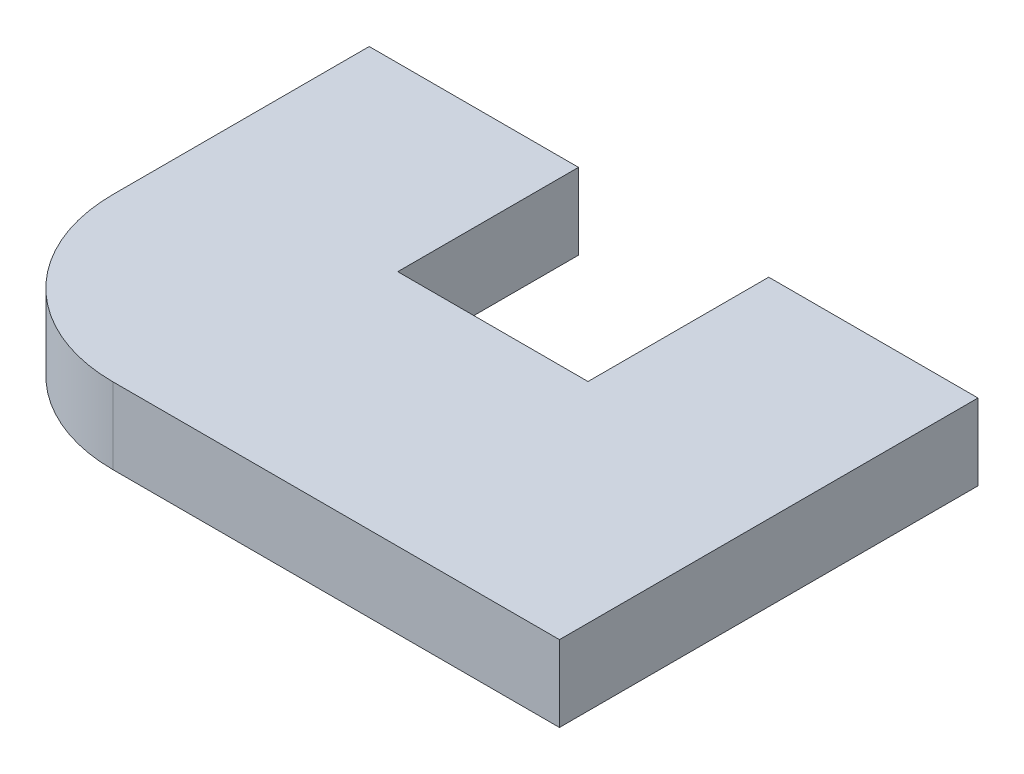
SolidWorks part; units mm, degrees
material "Ti-6Al-4VSolution treated and aged (SS)"
ref_plane "Front Plane" through (0, 0, 0) normal (0, 0, 1) x (1, 0, 0)
ref_plane "Top Plane" through (0, 0, 0) normal (0, 1, 0) x (1, 0, 0)
ref_plane "Right Plane" through (0, 0, 0) normal (1, 0, 0) x (0, 0, -1)
sketch "Sketch1" plane through (0, 0, 0) normal (0, 1, 0) x (1, 0, 0)
  line L1 (30.3553, -110) -> (55, -110)
  line L2 (-55, -24.6447) -> (-55, 110)
  line L3 (-55, 110) -> (55, 110)
  line L4 (55, -110) -> (55, 110)
  line L5 (-55, -110) -> (55, 110) construction
  line L6 (-55, 110) -> (55, -110) construction
  line L7 (55, -110) -> (155, -110)
  line L8 (55, -110) -> (55, 15)
  line L9 (55, 15) -> (155, 15)
  line L10 (155, -110) -> (155, 15)
  line L11 (155, -110) -> (265, -110)
  line L12 (155, -110) -> (155, 110)
  line L13 (155, 110) -> (265, 110)
  line L14 (265, -110) -> (265, 110)
  line L15 (-55, -110) -> (-30, -110) construction
  line L16 (-55, -110) -> (-55, -85) construction
  line L17 (-55, -85) -> (-30, -85) construction
  line L18 (-30, -110) -> (-30, -85) construction
  arc A0 (30.3553, -110) -> (-55, -24.6447) centre (30.3553, -24.6447) cw
  point P0 (0, 0)
  dimension "D1" = 25
  dimension "D2" = 220
  dimension "D3" = 100
  dimension "D4" = 125
  dimension "D5" = 210
  dimension "D6" = 25
extrude "Boss-Extrude1" add sketch "Sketch1" along normal blind 40 contours L1 L4 L3 L2 | L7 L10 L9 L4 | L11 L14 L13 L12 L10
fillet "Fillet1" [suppressed] radius 10
fillet "Fillet2" [suppressed] radius 20
sketch "Sketch2" plane through (0, 0, 0) normal (0, 1, 0) x (1, 0, 0)
  line L0 (55, -110) -> (155, -110) construction
  line L2 (55, 15) -> (155, 15) construction
  line L4 (155, -110) -> (265, -110) construction
  line L5 (265, -110) -> (265, 110) construction
  line L6 (155, 110) -> (265, 110) construction
  line L7 (155, -110) -> (155, 110) construction
  line L8 (55, -110) -> (55, 110) construction
  line L9 (-55, 110) -> (55, 110) construction
  line L10 (-55, -24.6447) -> (-55, 110) construction
  line L11 (30.3553, -110) -> (55, -110) construction
  line L12 (55, -110) -> (155, -110)
  line L14 (55, 15) -> (155, 15)
  line L16 (155, -110) -> (265, -110)
  line L17 (265, -110) -> (265, 110)
  line L18 (155, 110) -> (265, 110)
  line L19 (155, 15) -> (155, 110)
  line L20 (55, 15) -> (55, 110)
  line L21 (-55, 110) -> (55, 110)
  line L22 (-55, -24.6447) -> (-55, 110)
  line L23 (30.3553, -110) -> (55, -110)
  arc A0 (-55, -24.6447) -> (30.3553, -110) centre (30.3553, -24.6447) ccw construction
  arc A1 (-55, -24.6447) -> (30.3553, -110) centre (30.3553, -24.6447) ccw
extrude "Boss-Extrude2" [suppressed] add sketch "Sketch2" along normal up to surface (40 mm away) separate body
shell "Shell4" [suppressed] thickness 2.54
shell "Shell5" [suppressed] thickness 2.54
